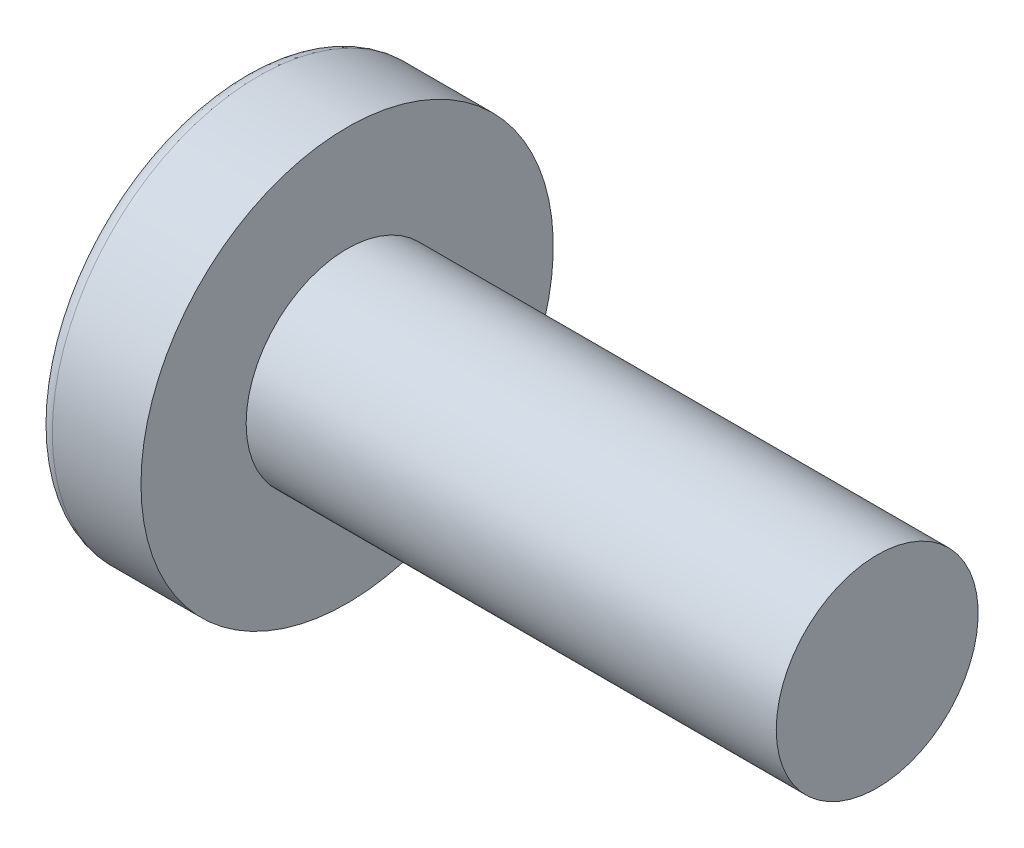
SolidWorks part; units mm, degrees
ref_plane "Plane1" through (0, 0, 0) normal (0, 0, 1) x (1, 0, 0)
ref_plane "Plane2" through (0, 0, 0) normal (0, 1, 0) x (1, 0, 0)
ref_plane "Plane3" through (0, 0, 0) normal (1, 0, 0) x (0, 0, -1)
sketch "BodySke" plane through (0, 0, 0) normal (0, 0, 1) x (1, 0, 0)
  line L0 (3, 2.4) -> (3, 4.9)
  line L1 (3.5, 6.35) -> (3.5, -3.175) construction
  line L2 (-25.4, 0) -> (127, 0) construction
  line L3 (15.6, 0) -> (0, 0)
  line L4 (3, 2.4) -> (15.6, 2.4)
  line L5 (15.6, 2.4) -> (15.6, 0)
  line L6 (0.8919, 4.9) -> (3, 4.9)
  line L7 (3, -2.4) -> (15.6, -2.4) construction
  line L8 (8.16, 6.35) -> (8.16, -3.175) construction
  arc A0 (0.5417, 4.6232) -> (0, 0) centre (20, 0) ccw
  arc A2 (0.5417, 4.6232) -> (0.8919, 4.9) centre (0.8919, 4.54) cw
  dimension "Head_crown_rad" = 20
  dimension "Head_fillet_rad" = 0.36
  dimension "Diameter" = 4.8
  dimension "Length" = 12.6
  dimension "Head_ht" = 3
  dimension "Head_dia" = 9.8
  dimension "Advance" = 0.5
  dimension "Thread_nom" = 7.44
revolve "Base-Revolve" add sketch "BodySke" angle 360 about L2
cosmetic thread "ThreadCosmetic" [suppressed] parameters "Thread_length"=7.44, "Thread_minor"=2.439
sketch "Sketch3" plane through (0, 0, 0) normal (1, 0, 0) x (0, 0, -1)
  line L0 (0.37, -1.45) -> (-0.37, -1.45)
  line L1 (0.37, -1.45) -> (0.37, 1.45)
  line L2 (-0.37, 1.45) -> (0.37, 1.45)
  line L3 (-0.37, 1.45) -> (-0.37, -1.45)
  dimension "Cross_dia" = 2.9
  dimension "D1" = 1.45
  dimension "Cross_width" = 0.74
  dimension "D2" = 0.37
ref_plane "Plane4" through (1.76, 0, 0) normal (1, 0, 0) x (0, 0, -1)
sketch "Sketch4" plane through (1.76, 0, 0) normal (1, 0, 0) x (0, 0, -1)
  line L0 (0.185, -0.185) -> (-0.185, -0.185)
  line L1 (0.185, -0.185) -> (0.185, 0.185)
  line L2 (-0.185, 0.185) -> (0.185, 0.185)
  line L3 (-0.185, 0.185) -> (-0.185, -0.185)
  dimension "D2" = 0.37
  dimension "D1" = 0.37
  dimension "D3" = 0.185
  dimension "D4" = 0.185
loft "Cut-Loft1" cut profiles "Sketch3", "Sketch4"
pattern_circular "CirPattern1" [suppressed] count 2 every 90 about axis through (-25.4, 0, 0) along (1, 0, 0)
sketch "ThdSchSke" plane through (0, 0, 0) normal (0, 0, 1) x (1, 0, 0)
  line L0 (8.16, -1.2195) -> (7.3334, -2.4)
  line L1 (8.16, -1.2195) -> (8.9866, -2.4)
  line L2 (8.9866, -2.4) -> (8.9866, -3)
  line L3 (-3.175, 0) -> (5.1513, 0) construction
  line L5 (8.9866, -3) -> (7.3334, -3)
  line L6 (7.3334, -3) -> (7.3334, -2.4)
  dimension "Diameter" = 4.8
  dimension "SideAngle" = 55
  dimension "VeeAngle" = 70
  dimension "Thread_minor" = 2.439
  dimension "Overcut" = 6
  dimension "Start" = 8.16
revolve "ThreadSchematic" [suppressed] cut sketch "ThdSchSke" angle 360 about L3
pattern_linear "ThdSchPat" [suppressed]
equation "\"D1@Sketch3\" = \"Cross_dia@Sketch3\" / 2"
equation "\"D2@Sketch3\" = \"Cross_width@Sketch3\" / 2"
equation "\"D1@Sketch4\" = \"Cross_width@Sketch3\" *.5"
equation "\"D2@Sketch4\" = \"D1@Sketch4\""
equation "\"D3@Sketch4\" = \"D1@Sketch4\" / 2"
equation "\"D4@Sketch4\" = \"D2@Sketch4\" / 2"
equation "\"Thread_length@ThreadCosmetic\" = ((sgn( (\"Length@BodySke\" - \"Advance@BodySke\" ) - \"Thread_nom@BodySke\" )-1)*( (\"Length@BodySke\" - \"Advance@BodySke\" ) - \"Thread_nom@BodySke\" ))/-2+ \"Thread_nom@BodySke\""
equation "\"Thread_minor@ThdSchSke\" = \"Thread_minor@ThreadCosmetic\""
equation "\"Diameter@ThdSchSke\" = \"Diameter@BodySke\""
equation "\"Overcut@ThdSchSke\" = \"Diameter@BodySke\" * 1.25"
equation "\"Start@ThdSchSke\" = \"Head_ht@BodySke\" + \"Length@BodySke\" - \"Thread_length@ThreadCosmetic\"  '---Non-countersunk---"
equation "\"Num_threads@ThdSchPat\" = int( \"Thread_length@ThreadCosmetic\" / \"Advance@BodySke\" + 0.999 )  + 1"
equation "\"Advance@ThdSchPat\" = \"Thread_length@ThreadCosmetic\" /  (\"Num_threads@ThdSchPat\" - 1) 'relax it"
